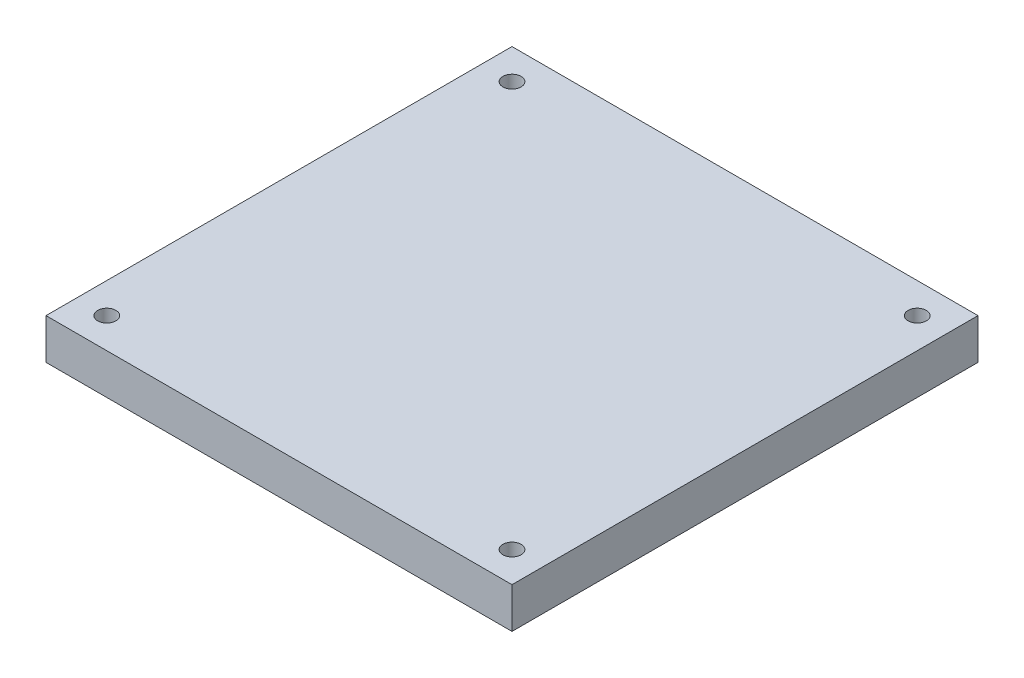
SolidWorks part; units mm, degrees
ref_plane "Front Plane" through (0, 0, 0) normal (0, 0, 1) x (1, 0, 0)
ref_plane "Top Plane" through (0, 0, 0) normal (0, 1, 0) x (1, 0, 0)
ref_plane "Right Plane" through (0, 0, 0) normal (1, 0, 0) x (0, 0, -1)
sketch "Sketch2" plane through (0, 0, 0) normal (0, 1, 0) x (1, 0, 0)
  line L1 (0, 0) -> (115, 0)
  line L2 (0, 0) -> (0, 115)
  line L3 (0, 115) -> (115, 115)
  line L4 (115, 0) -> (115, 115)
  circle A0 centre (7.5, 7.5) radius 2.25
  circle A1 centre (107.5, 7.5) radius 2.25
  circle A2 centre (107.5, 107.5) radius 2.25
  circle A3 centre (7.5, 107.5) radius 2.25
  dimension "D4" = 4.5
  dimension "D1" = 115
  dimension "D2" = 115
  dimension "D7" = 100
  dimension "D8" = 100
  dimension "D9" = 100
  dimension "D10" = 7.5
  dimension "D11" = 7.5
extrude "Boss-Extrude1" add sketch "Sketch2" along normal blind 10
